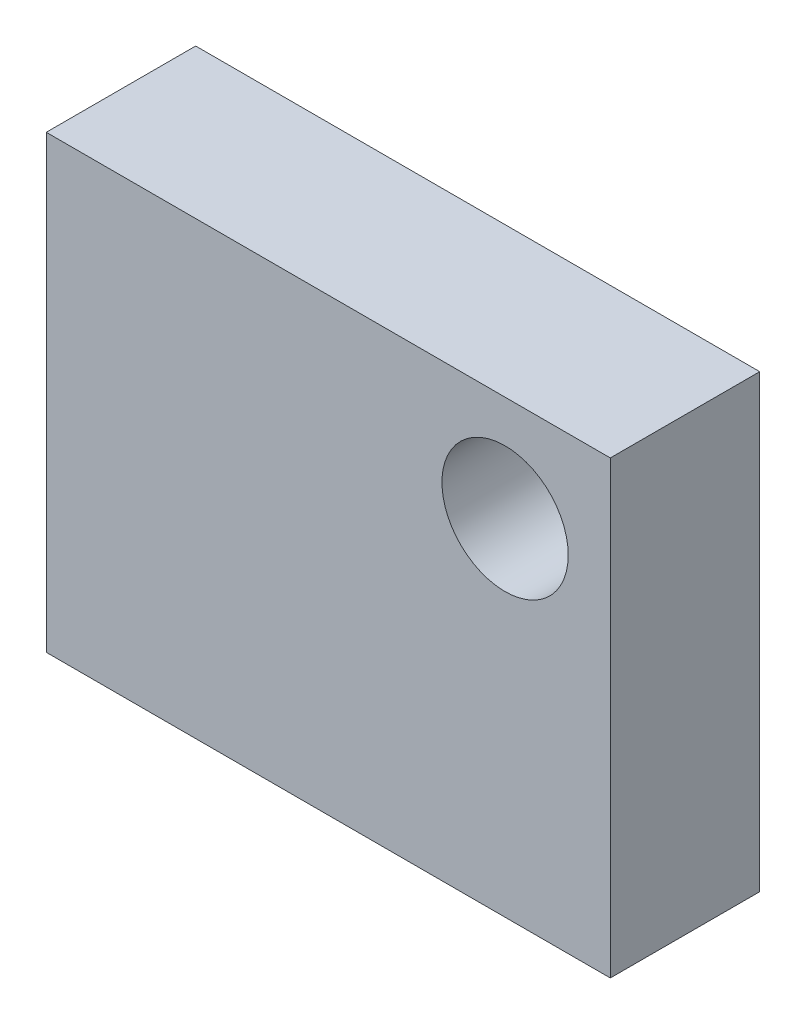
SolidWorks part; units mm, degrees
ref_plane "Ön Düzlem" through (0, 0, 0) normal (0, 0, 1) x (1, 0, 0)
ref_plane "Üst Düzlem" through (0, 0, 0) normal (0, 1, 0) x (1, 0, 0)
ref_plane "Sağ Düzlem" through (0, 0, 0) normal (1, 0, 0) x (0, 0, -1)
sketch "Sketch1" plane through (0, 0, 0) normal (0, 0, 1) x (1, 0, 0)
  line L1 (-6.7, 5.35) -> (6.7, 5.35)
  line L2 (-6.7, 5.35) -> (-6.7, -5.35)
  line L3 (-6.7, -5.35) -> (6.7, -5.35)
  line L4 (6.7, 5.35) -> (6.7, -5.35)
  line L5 (-6.7, 5.35) -> (6.7, -5.35) construction
  line L6 (-6.7, -5.35) -> (6.7, 5.35) construction
  point P0 (0, 0)
  dimension "D1" = 13.4
  dimension "D2" = 10.7
extrude "Boss-Extrude1" add sketch "Sketch1" along normal blind 3.55
sketch "Sketch2" plane through (0, 0, 3.55) normal (0, 0, 1) x (1, 0, 0)
  line L1 (6.7, 5.35) -> (-6.7, 5.35) construction
  line L2 (6.7, -5.35) -> (6.7, 5.35) construction
  circle A0 centre (4.2, 2.85) radius 1.5
  dimension "D1" = 3
  dimension "D2" = 2.5
  dimension "D3" = 2.5
extrude "Cut-Extrude1" cut sketch "Sketch2" against normal blind 3.55
